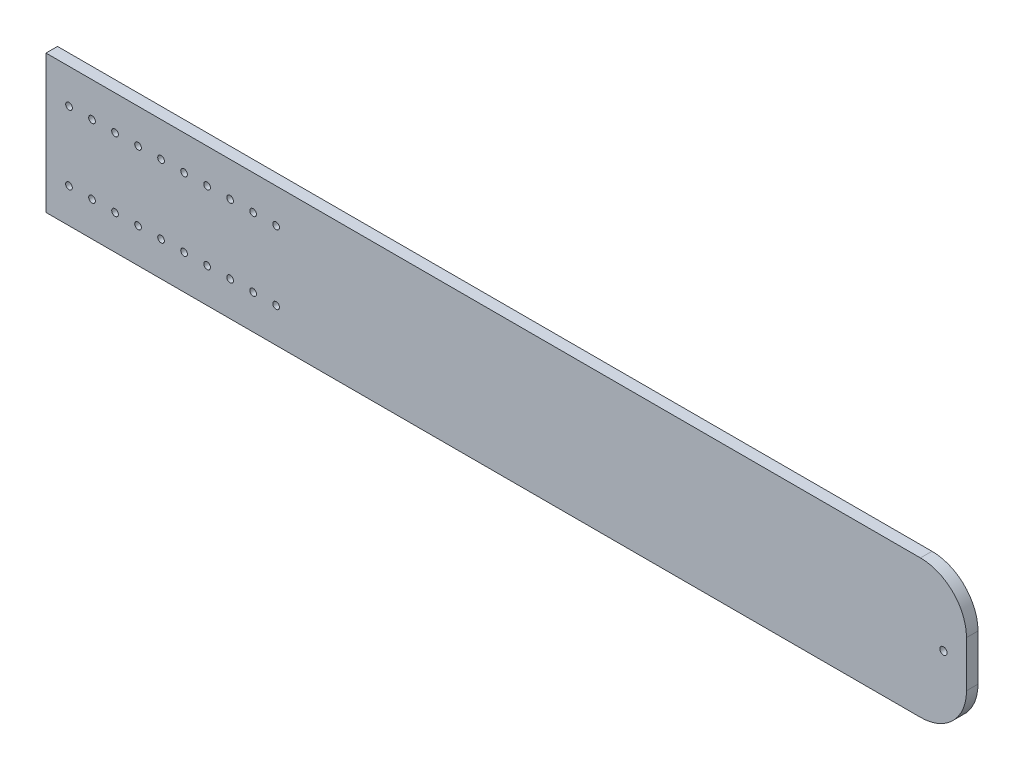
SolidWorks part; units mm, degrees
ref_plane "Front" through (0, 0, 0) normal (0, 0, 1) x (1, 0, 0)
ref_plane "Top" through (0, 0, 0) normal (0, 1, 0) x (1, 0, 0)
ref_plane "Right" through (0, 0, 0) normal (1, 0, 0) x (0, 0, -1)
sketch "Sketch1" plane through (0, 0, 0) normal (0, 0, 1) x (1, 0, 0)
  line L1 (0, 0) -> (508, 0)
  line L2 (0, 0) -> (0, 76.2)
  line L3 (0, 76.2) -> (508, 76.2)
  line L4 (508, 0) -> (508, 76.2)
  dimension "D1" = 508
  dimension "D2" = 76.2
extrude "basic_plank" add sketch "Sketch1" along normal blind 6.35
sketch "Sketch2" plane through (0, 0, 6.35) normal (0, 0, 1) x (1, 0, 0)
  line L0 (508, 76.2) -> (0, 76.2) construction
  line L3 (0, 76.2) -> (0, 0) construction
  circle A0 centre (12.7, 57.15) radius 1.8415
  circle A1 centre (25.4, 57.15) radius 1.8415
  circle A2 centre (38.1, 57.15) radius 1.8415
  circle A3 centre (50.8, 57.15) radius 1.8415
  circle A4 centre (63.5, 57.15) radius 1.8415
  circle A5 centre (76.2, 57.15) radius 1.8415
  circle A6 centre (88.9, 57.15) radius 1.8415
  circle A7 centre (101.6, 57.15) radius 1.8415
  circle A8 centre (114.3, 57.15) radius 1.8415
  circle A9 centre (127, 57.15) radius 1.8415
  circle A10 centre (12.7, 19.05) radius 1.8415
  circle A11 centre (25.4, 19.05) radius 1.8415
  circle A12 centre (38.1, 19.05) radius 1.8415
  circle A13 centre (50.8, 19.05) radius 1.8415
  circle A14 centre (63.5, 19.05) radius 1.8415
  circle A15 centre (76.2, 19.05) radius 1.8415
  circle A16 centre (88.9, 19.05) radius 1.8415
  circle A17 centre (101.6, 19.05) radius 1.8415
  circle A18 centre (114.3, 19.05) radius 1.8415
  circle A19 centre (127, 19.05) radius 1.8415
  dimension "D1" = 3.683
  dimension "D2" = 19.05
  dimension "D3" = 12.7
  dimension "D4" = 10
  dimension "D5" = 2
extrude "placement holes" cut sketch "Sketch2" against normal through all
fillet "Fillet1" radius 25.4 2 edges at (508, 0, 3.175) (508, 76.2, 3.175)
sketch "Sketch3" plane through (0, 0, 6.35) normal (0, 0, 1) x (1, 0, 0)
  line L0 (508, 25.4) -> (508, 50.8) construction
  line L1 (482.6, 76.2) -> (0, 76.2) construction
  circle A0 centre (495.3, 38.1) radius 2.0066
  dimension "D1" = 4.0132
  dimension "D3" = 38.1
  dimension "D2" = 12.7
extrude "wheel_hole" cut sketch "Sketch3" against normal through all
